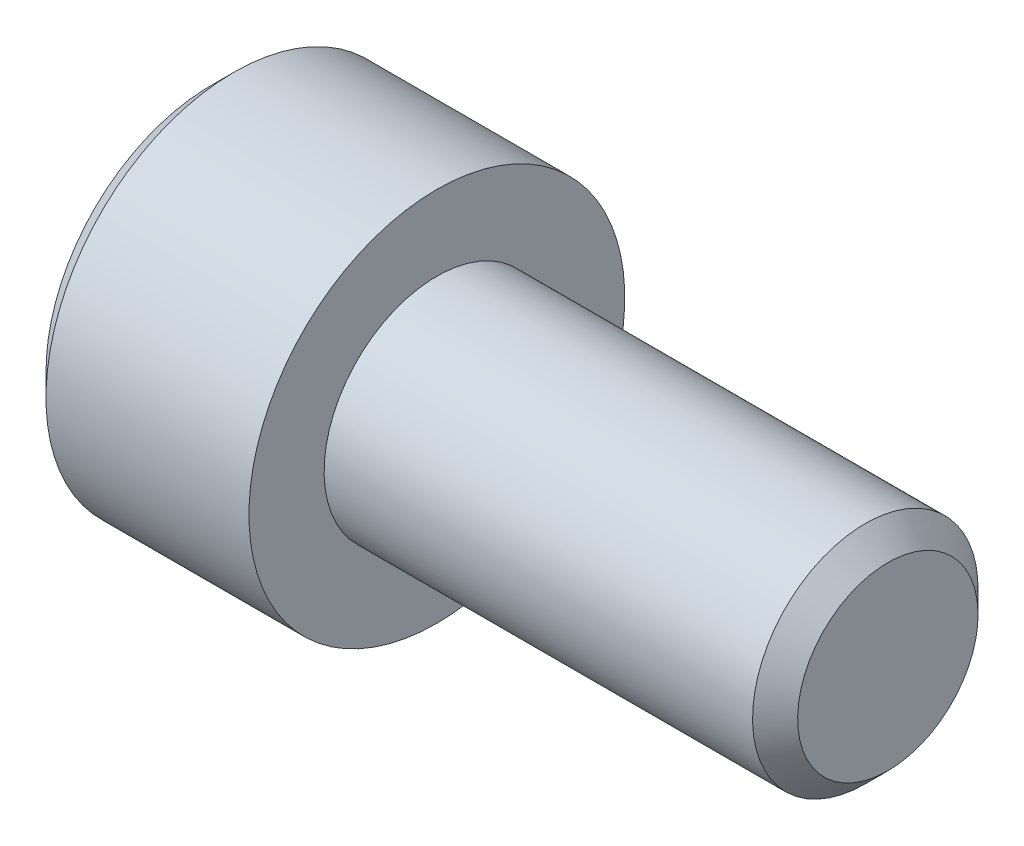
SolidWorks part; units mm, degrees
ref_plane "Front" through (0, 0, 0) normal (0, 0, 1) x (1, 0, 0)
ref_plane "Top" through (0, 0, 0) normal (0, 1, 0) x (1, 0, 0)
ref_plane "Right" through (0, 0, 0) normal (1, 0, 0) x (0, 0, -1)
ref_plane "Plane1" through (0, 0, 0) normal (0, 0, 1) x (1, 0, 0)
sketch "Sketch1" plane through (0, 0, 0) normal (0, 0, 1) x (1, 0, 0)
  line L0 (-6, 0) -> (-6, 4.4)
  line L1 (-6, 4.4) -> (-5.4, 5)
  line L2 (-5.4, 5) -> (0, 5)
  line L3 (0, 5) -> (0, 3)
  line L4 (0, 3) -> (12, 3)
  line L6 (12, 3) -> (12, 0)
  line L7 (12, 0) -> (-6, 0)
  line L8 (12, 0) -> (-6, 0) construction
  dimension "D1" = 12
  dimension "D2" = 3
  dimension "D3" = 5
  dimension "D4" = 6
revolve "Revolve1" add sketch "Sketch1" angle 360 about L8
ref_plane "Plane2" through (0, 0, 0) normal (0, 0, 1) x (1, 0, 0)
chamfer "Chamfer1" distance 0.6 angle 45 1 edges at (12, -3, 0)
sketch "Sketch2" plane through (0, 0, 0) normal (0, 0, 1) x (1, 0, 0)
  line L0 (-6, 0) -> (-6, 2.5)
  line L1 (-6, 2.5) -> (-3, 2.5)
  line L2 (-3, 2.5) -> (-2.3301, 0)
  line L3 (-2.3301, 0) -> (-6, 0)
  line L4 (-2.3301, 0) -> (-6, 0) construction
revolve "Cut-Revolve1" cut sketch "Sketch2" angle 360 about L4
ref_plane "Plane3" through (-6, 0, 0) normal (1, 0, 0) x (0, 0, -1)
sketch "Sketch3" plane through (-6, 0, 0) normal (1, 0, 0) x (0, 0, -1)
  line L0 (-2.5, 1.4434) -> (-2.5, -1.4434)
  line L1 (-2.5, -1.4434) -> (0, -2.8868)
  line L2 (0, -2.8868) -> (2.5, -1.4434)
  line L3 (2.5, -1.4434) -> (2.5, 1.4434)
  line L4 (2.5, 1.4434) -> (0, 2.8868)
  line L5 (0, 2.8868) -> (-2.5, 1.4434)
extrude "Cut-Extrude1" cut sketch "Sketch3" along normal blind 3
